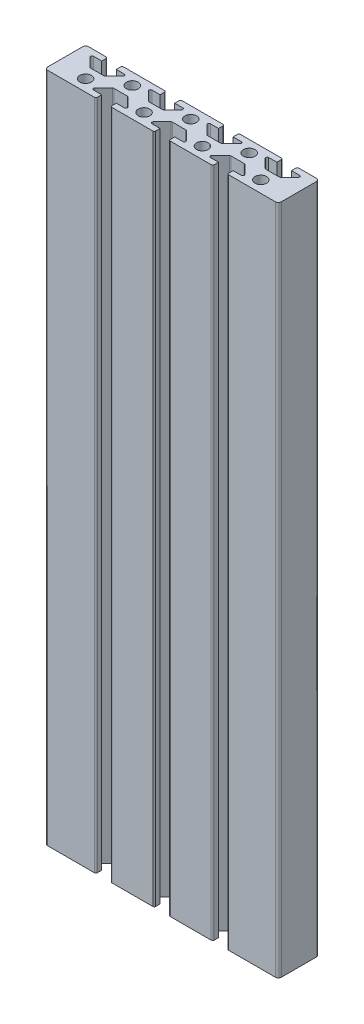
SolidWorks part; units mm, degrees
ref_plane "Front Plane" through (0, 0, 0) normal (0, 0, 1) x (1, 0, 0)
ref_plane "Top Plane" through (0, 0, 0) normal (0, 1, 0) x (1, 0, 0)
ref_plane "Right Plane" through (0, 0, 0) normal (1, 0, 0) x (0, 0, -1)
sketch "Sketch1" plane through (0, 0, 0) normal (0, 1, 0) x (1, 0, 0)
  line L0 (63.5, 12) -> (67.5, 12)
  line L1 (0, 0) -> (80, 0)
  line L2 (0, 0) -> (0, 14)
  line L3 (0, 14) -> (80, 14)
  line L4 (80, 0) -> (80, 14)
  line L5 (67.5, 12) -> (67.5, 14)
  line L6 (67.5, 14) -> (72.5, 14)
  line L7 (72.5, 14) -> (72.5, 12)
  line L9 (76.5, 12) -> (72.5, 8)
  line L10 (72.5, 8) -> (67.5, 8)
  line L11 (67.5, 8) -> (63.5, 12)
  line L12 (72.5, 12) -> (76.5, 12)
  line L13 (52.5, 12) -> (56.5, 12)
  line L14 (56.5, 12) -> (52.5, 8)
  line L15 (52.5, 8) -> (47.5, 8)
  line L16 (47.5, 8) -> (43.5, 12)
  line L17 (43.5, 12) -> (47.5, 12)
  line L18 (47.5, 12) -> (47.5, 14)
  line L19 (47.5, 14) -> (52.5, 14)
  line L20 (52.5, 14) -> (52.5, 12)
  line L21 (32.5, 12) -> (36.5, 12)
  line L22 (36.5, 12) -> (32.5, 8)
  line L23 (32.5, 8) -> (27.5, 8)
  line L24 (27.5, 8) -> (23.5, 12)
  line L25 (23.5, 12) -> (27.5, 12)
  line L26 (27.5, 12) -> (27.5, 14)
  line L27 (27.5, 14) -> (32.5, 14)
  line L28 (32.5, 14) -> (32.5, 12)
  line L29 (12.5, 12) -> (16.5, 12)
  line L30 (16.5, 12) -> (12.5, 8)
  line L31 (12.5, 8) -> (7.5, 8)
  line L32 (7.5, 8) -> (3.5, 12)
  line L33 (3.5, 12) -> (7.5, 12)
  line L34 (7.5, 12) -> (7.5, 14)
  line L35 (7.5, 14) -> (12.5, 14)
  line L36 (12.5, 14) -> (12.5, 12)
  line L37 (57.5, 0) -> (57.5, 2)
  line L38 (57.5, 2) -> (53.5, 2)
  line L39 (53.5, 2) -> (57.5, 6)
  line L40 (57.5, 6) -> (62.5, 6)
  line L41 (62.5, 6) -> (66.5, 2)
  line L42 (66.5, 2) -> (62.5, 2)
  line L43 (62.5, 2) -> (62.5, 0)
  line L44 (62.5, 0) -> (57.5, 0)
  line L45 (42.5, 0) -> (37.5, 0)
  line L46 (37.5, 0) -> (37.5, 2)
  line L47 (37.5, 2) -> (33.5, 2)
  line L48 (33.5, 2) -> (37.5, 6)
  line L49 (37.5, 6) -> (42.5, 6)
  line L50 (42.5, 6) -> (46.5, 2)
  line L51 (46.5, 2) -> (42.5, 2)
  line L52 (42.5, 2) -> (42.5, 0)
  line L53 (22.5, 0) -> (17.5, 0)
  line L54 (17.5, 0) -> (17.5, 2)
  line L55 (17.5, 2) -> (13.5, 2)
  line L56 (13.5, 2) -> (17.5, 6)
  line L57 (17.5, 6) -> (22.5, 6)
  line L58 (22.5, 6) -> (26.5, 2)
  line L59 (26.5, 2) -> (22.5, 2)
  line L60 (22.5, 2) -> (22.5, 0)
  circle A0 centre (60, 10) radius 2
  circle A1 centre (40, 10) radius 2
  circle A2 centre (20, 10) radius 2
  circle A3 centre (70, 4) radius 2
  circle A4 centre (50, 4) radius 2
  circle A5 centre (30, 4) radius 2
  circle A6 centre (10, 4) radius 2
  dimension "D17" = 4
  dimension "D21" = 4
  dimension "D1" = 80
  dimension "D2" = 14
  dimension "D3" = 7.5
  dimension "D4" = 5
  dimension "D5" = 6
  dimension "D6" = 17.5
  dimension "D7" = 2
  dimension "D8" = 4
  dimension "D9" = 5
  dimension "D10" = 5
  dimension "D11" = 4
  dimension "D12" = 4
  dimension "D13" = 2
  dimension "D14" = 2
  dimension "D15" = 6
  dimension "D16" = 3
  dimension "D18" = 20
  dimension "D19" = 4
  dimension "D22" = 10
  dimension "D23" = 4
  dimension "D20" = 3
  dimension "D24" = 4
extrude "Boss-Extrude1" add sketch "Sketch1" along normal blind 230 contours L59 L60 L1 L46 L47 L48 L49 L50 L51 L52 L37 L38 L39 L40 L41 L42 L43 L4 L3 L7 L12 L9 L10 L11 L0 L5 L20 L13 L14 L15 L16 L17 L18 L28 L21 L22 L23 L24 L25 L26 L36 L29 L30 L31 L32 L33
fillet "Fillet1" radius 0.5 24 edges at (67.5, 115, -8) (63.5, 115, -12) (76.5, 115, -12) (72.5, 115, -8) (47.5, 115, -8) (27.5, 115, -8) (52.5, 115, -8) (32.5, 115, -8) (56.5, 115, -12) (36.5, 115, -12) (43.5, 115, -12) (23.5, 115, -12) (12.5, 115, -8) (7.5, 115, -8) (3.5, 115, -12) (16.5, 115, -12) (72.5, 115, -14) (67.5, 115, -14) (52.5, 115, -14) (47.5, 115, -14) (32.5, 115, -14) (27.5, 115, -14) (12.5, 115, -14) (7.5, 115, -14)
fillet "Fillet2" radius 0.5 18 edges at (17.5, 115, -6) (26.5, 115, -2) (22.5, 115, -6) (22.5, 115, 0) (17.5, 115, 0) (13.5, 115, -2) (33.5, 115, -2) (37.5, 115, -6) (42.5, 115, -6) (42.5, 115, 0) (46.5, 115, -2) (37.5, 115, 0) (57.5, 115, 0) (62.5, 115, 0) (53.5, 115, -2) (57.5, 115, -6) (66.5, 115, -2) (62.5, 115, -6)
fillet "Fillet3" radius 1 4 edges at (0, 115, -14) (0, 115, 0) (80, 115, -14) (80, 115, 0)
sketch "Sketch2" plane through (0, 0, -14) normal (0, 0, -1) x (-1, 0, 0)
  line L0 (-33, 0) -> (-47, 0) construction
  circle A1 centre (-40, 10) radius 2.5
  dimension "D1" = 10
  dimension "D2" = 5
extrude "Cut-Extrude2" cut sketch "Sketch2" against normal blind 230 contours A1
sketch "Sketch3" plane through (0, 0, -14) normal (0, 0, -1) x (-1, 0, 0)
  circle A0 centre (-40, 10) radius 5.5
  dimension "D1" = 11
extrude "Cut-Extrude3" cut sketch "Sketch3" against normal blind 7 contours A0
sketch "Sketch4" plane through (0, 0, -14) normal (0, 0, -1) x (-1, 0, 0)
  line L0 (-33, 230) -> (-47, 230) construction
  circle A0 centre (-40, 220) radius 2.5
  dimension "D1" = 5
  dimension "D2" = 10
extrude "Cut-Extrude4" cut sketch "Sketch4" against normal blind 7
sketch "Sketch5" plane through (0, 0, -14) normal (0, 0, -1) x (-1, 0, 0)
  circle A0 centre (-40, 220) radius 5.5
  dimension "D1" = 11
extrude "Cut-Extrude5" cut sketch "Sketch5" against normal blind 7
